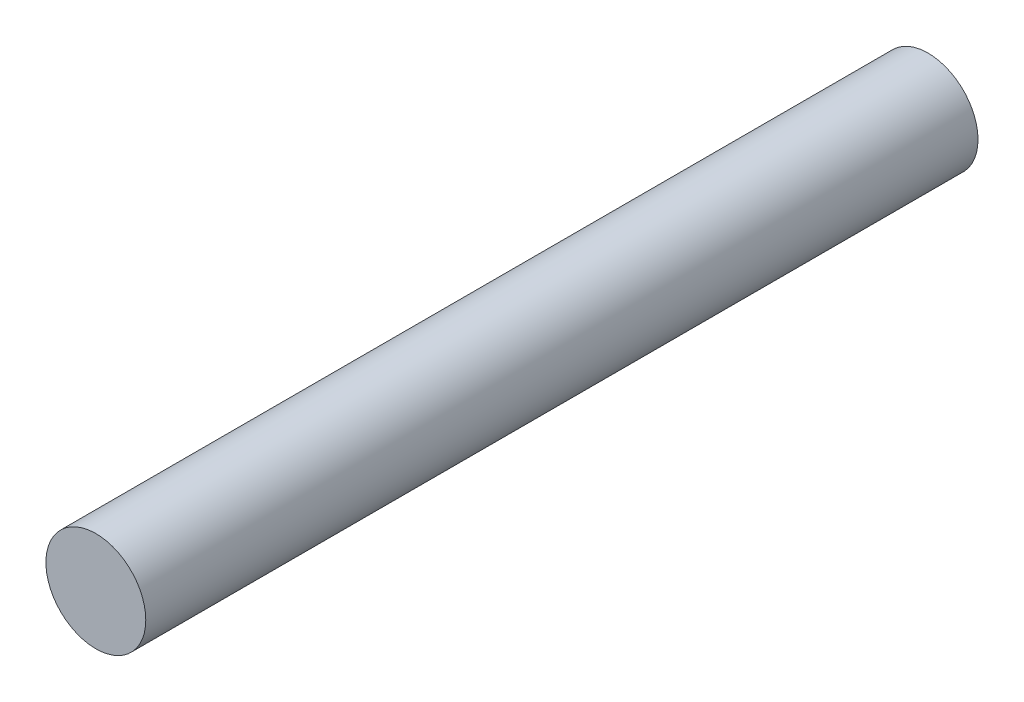
SolidWorks part; units mm, degrees
material "AISI 1020"
ref_plane "Front Plane" through (0, 0, 0) normal (0, 0, 1) x (1, 0, 0)
ref_plane "Top Plane" through (0, 0, 0) normal (0, 1, 0) x (1, 0, 0)
ref_plane "Right Plane" through (0, 0, 0) normal (1, 0, 0) x (0, 0, -1)
sketch "Sketch1" plane through (0, 0, 0) normal (0, 0, 1) x (1, 0, 0)
  circle A0 centre (0, 0) radius 6
  dimension "D1" = 12
extrude "Boss-Extrude1" add sketch "Sketch1" along normal mid plane 100
